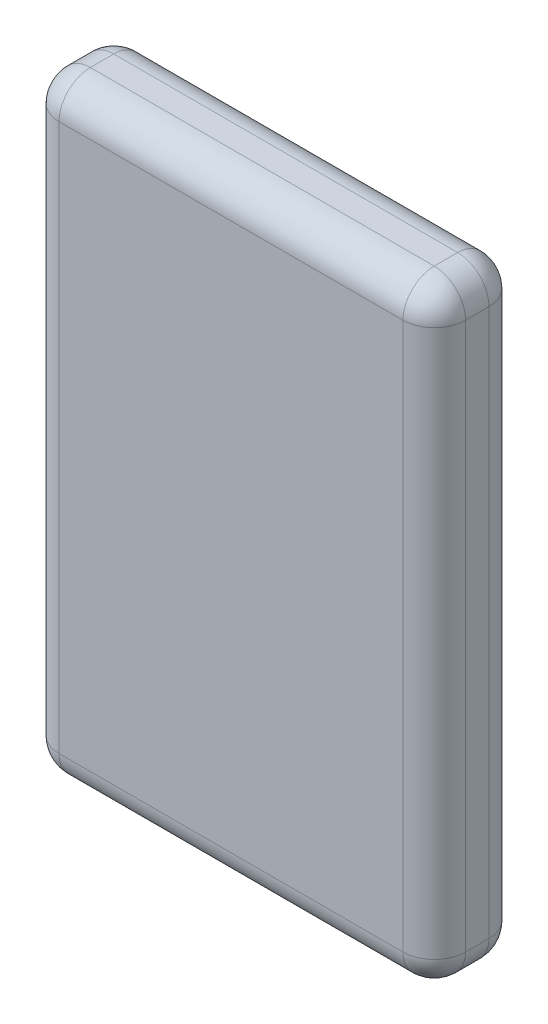
SolidWorks part; units mm, degrees
ref_plane "Front Plane" through (0, 0, 0) normal (0, 0, 1) x (1, 0, 0)
ref_plane "Top Plane" through (0, 0, 0) normal (0, 1, 0) x (1, 0, 0)
ref_plane "Right Plane" through (0, 0, 0) normal (1, 0, 0) x (0, 0, -1)
sketch "Sketch1" plane through (0, 0, 0) normal (0, 0, 1) x (1, 0, 0)
  line L1 (-13, 21.7258) -> (13, 21.7258)
  line L2 (-13, 21.7258) -> (-13, -17.2742)
  line L3 (-13, -17.2742) -> (13, -17.2742)
  line L4 (13, 21.7258) -> (13, -17.2742)
  line L5 (-13, 21.7258) -> (13, -17.2742) construction
  line L6 (-13, -17.2742) -> (13, 21.7258) construction
  point P0 (0, 2.2258)
  dimension "D1" = 39
  dimension "D2" = 26
  dimension "D3" = 0.5
extrude "Boss-Extrude1" add sketch "Sketch1" along normal blind 5.5 from offset 2.2
fillet "Fillet1" radius 2 12 edges at (13, -17.2742, 4.95) (0, -17.2742, 7.7) (13, 2.2258, 7.7) (-13, 2.2258, 7.7) (-13, -17.2742, 4.95) (13, 21.7258, 4.95) (0, 21.7258, 7.7) (-13, 21.7258, 4.95) (0, 21.7258, 2.2) (-13, 2.2258, 2.2) (0, -17.2742, 2.2) (13, 2.2258, 2.2)
